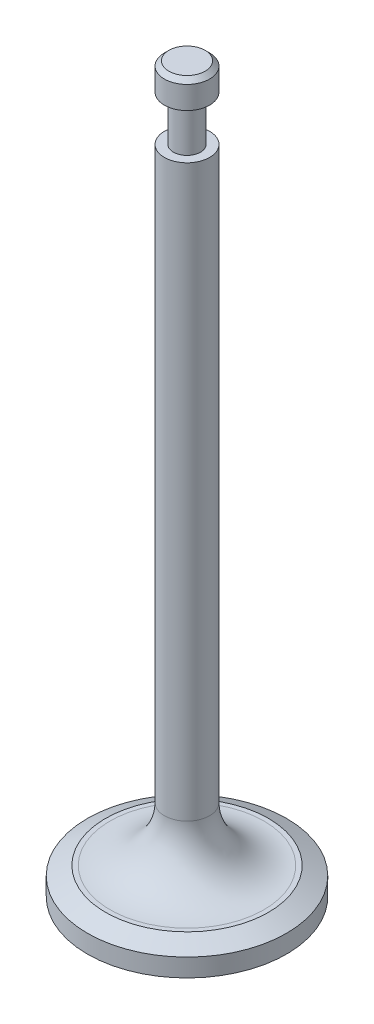
SolidWorks part; units mm, degrees
ref_plane "Front Plane" through (0, 0, 0) normal (0, 0, 1) x (1, 0, 0)
ref_plane "Top Plane" through (0, 0, 0) normal (0, 1, 0) x (1, 0, 0)
ref_plane "Right Plane" through (0, 0, 0) normal (1, 0, 0) x (0, 0, -1)
sketch "Sketch1" plane through (0, 0, 0) normal (1, 0, 0) x (0, 0, -1)
  line L0 (0, 0) -> (0, -80)
  line L1 (0, -80) -> (11, -80)
  line L2 (11, -80) -> (11, -77)
  line L3 (11, -77) -> (2.5, -77)
  line L4 (2.5, -77) -> (2.5, -8)
  line L5 (2.5, -8) -> (1.5, -8)
  line L6 (1.5, -8) -> (1.5, -3)
  line L7 (1.5, -3) -> (2.5, -3)
  line L8 (2.5, -3) -> (2.5, 0)
  line L9 (2.5, 0) -> (0, 0)
  dimension "D1" = 80
  dimension "D2" = 11
  dimension "D3" = 3
  dimension "D4" = 2.5
  dimension "D5" = 3
  dimension "D6" = 5
  dimension "D7" = 1
  dimension "D8" = 2.5
revolve "Revolve1" add sketch "Sketch1" angle 360 about L0
fillet "Fillet2" radius 6 1 edges at (0, -77, 2.5)
chamfer "Chamfer1" distance 1 distance2 2 1 edges at (0, -77, 11)
chamfer "Chamfer2" distance 0.5 angle 45 1 edges at (0, 0, 2.5)
